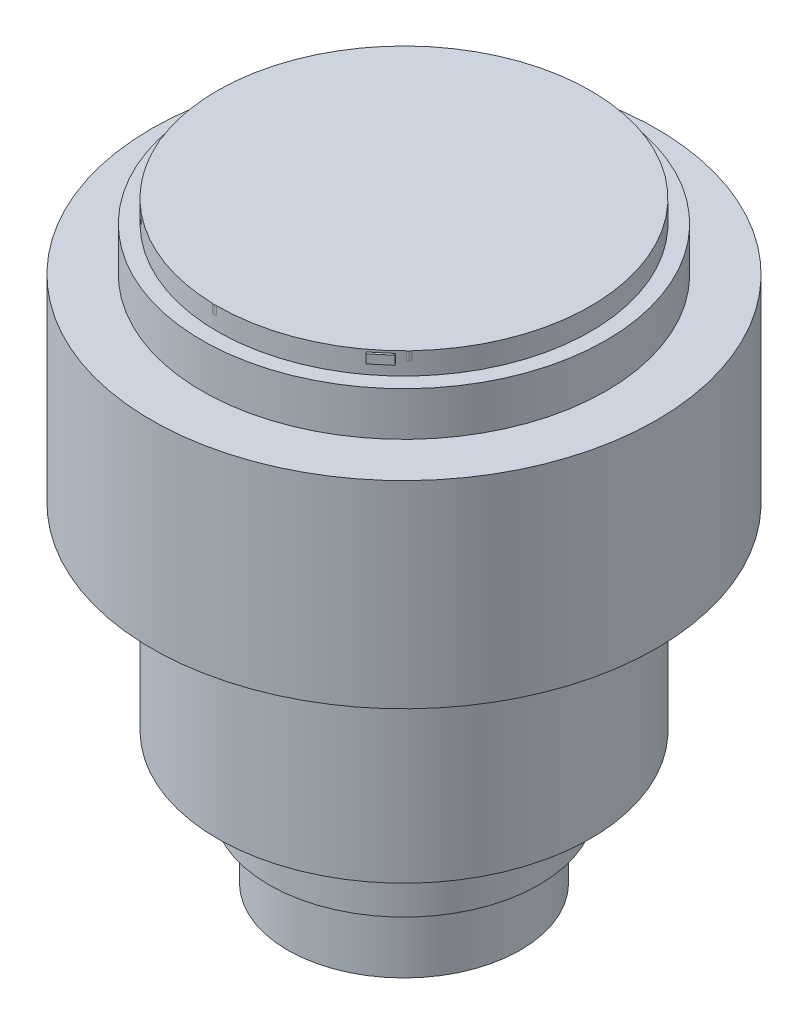
SolidWorks part; units mm, degrees
material "ABS"
ref_plane "Front Plane" through (0, 0, 0) normal (0, 0, 1) x (1, 0, 0)
ref_plane "Top Plane" through (0, 0, 0) normal (0, 1, 0) x (1, 0, 0)
ref_plane "Right Plane" through (0, 0, 0) normal (1, 0, 0) x (0, 0, -1)
sketch "Sketch1" plane through (0, 0, 0) normal (0, 0, 1) x (1, 0, 0)
  line L0 (0, 56.497) -> (0, -78.503) construction
  line L1 (0, 56.497) -> (42.5, 56.497) construction
  line L2 (0, 51.497) -> (42.5, 51.497) construction
  line L3 (0, -48.503) -> (30.75, -48.503) construction
  line L4 (0, -3.503) -> (42.5, -3.503) construction
  line L5 (0, 22.1791) -> (47.5, 22.1791) construction
  line L6 (0, 41.497) -> (46, 41.497) construction
  line L7 (0, -78.503) -> (26.5, -78.503) construction
  line L8 (0, 36.497) -> (57.5, 36.497) construction
  line L9 (0, -63.503) -> (30.75, -63.503) construction
  dimension "D1" = 135
  dimension "D2" = 42.5
  dimension "D4" = 42.5
  dimension "D5" = 47.5
  dimension "D7" = 45
  dimension "D8" = 45
  dimension "D6" = 5
  dimension "D9" = 10
  dimension "D10" = 30
  dimension "D11" = 5
  dimension "D12" = 57.5
  dimension "D13" = 46
  dimension "D14" = 15
  dimension "D15" = 26.5
  dimension "D3" = 30.75
  dimension "D16" = 30.75
sketch "Sketch4" plane through (0, 0, 0) normal (0, 0, 1) x (1, 0, 0)
  line L0 (0, 56.497) -> (42.5, 56.497)
  line L1 (42.5, 56.497) -> (42.5, 51.497)
  line L2 (0, 51.497) -> (42.5, 51.497) construction
  line L3 (42.5, 51.497) -> (46, 51.497)
  line L4 (46, 51.497) -> (46, 41.497)
  line L5 (46, 41.497) -> (57.5, 41.497)
  line L6 (57.5, 41.497) -> (57.5, 36.497)
  line L7 (57.5, 36.497) -> (57.5, -3.503)
  line L10 (57.5, -3.503) -> (42.5, -3.503)
  line L11 (42.5, -3.503) -> (42.5, -48.503)
  line L12 (42.5, -48.503) -> (30.75, -48.503)
  line L13 (30.75, -48.503) -> (30.75, -63.503)
  line L14 (30.75, -63.503) -> (26.5, -63.503)
  line L15 (26.5, -63.503) -> (26.5, -78.503)
  line L16 (26.5, -78.503) -> (0, -78.503)
revolve "Revolve-Thin4" add sketch "Sketch4" angle 360 about L0
sketch "Sketch5" plane through (0, 56.497, 0) normal (0, 1, 0) x (1, 0, 0)
  text T0 "nikkor AFS 24-120mm F4_0 VR ED" font "Arial Narrow" height in points 28
extrude "Boss-Extrude2" add sketch "Sketch5" against normal offset from surface (2 mm away) 2 up to face at (-42.5, 56.497, 0)
equation "\"D5@Sketch1\"=95/2"
equation "\"D4@Sketch1\"=85/2"
equation "\"D2@Sketch1\"=85/2"
equation "\"D12@Sketch1\"=115/2"
equation "\"D13@Sketch1\"=92/2"
equation "\"D15@Sketch1\"=53/2"
equation "\"D3@Sketch1\"=(70+53)/4"
